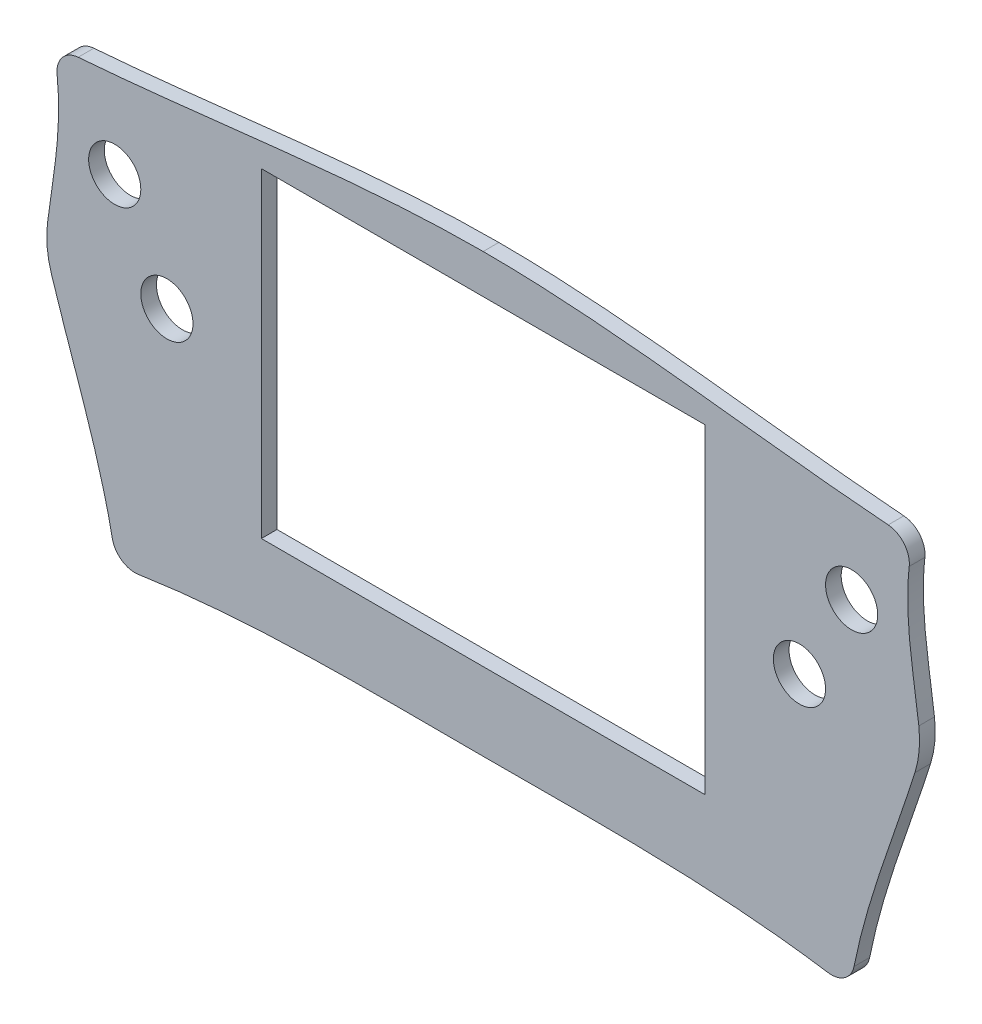
SolidWorks part; units mm, degrees
ref_plane "Front Plane" through (0, 0, 0) normal (0, 0, 1) x (1, 0, 0)
ref_plane "Top Plane" through (0, 0, 0) normal (0, 1, 0) x (1, 0, 0)
ref_plane "Right Plane" through (0, 0, 0) normal (1, 0, 0) x (0, 0, -1)
sketch "Sketch1" plane through (0, 0, 0) normal (0, 0, 1) x (1, 0, 0)
  line L0 (-89.6723, 78.6151) -> (-76.9723, 56.618) construction
  line L1 (-53.975, 97.6651) -> (53.975, 97.6651)
  line L2 (-53.975, 97.6651) -> (-53.975, 19.6871)
  line L3 (-53.975, 19.6871) -> (53.975, 19.6871)
  line L4 (53.975, 97.6651) -> (53.975, 19.6871)
  line L5 (77.0035, 56.618) -> (89.7035, 78.6151) construction
  line L6 (-1053.4632, 84.9651) -> (48946.5368, 84.9651) construction
  line L7 (-89.6723, 78.6151) -> (-98.1384, 93.2788) construction
  line L8 (89.7035, 78.6151) -> (98.1696, 93.2788) construction
  arc A0 (-90.9952, 1.4308) -> (-83.8129, -3.6021) centre (-84.7684, 2.6757) ccw construction
  arc A1 (91.0264, 1.4308) -> (83.8442, -3.6021) centre (84.7996, 2.6757) cw construction
  arc A2 (104.4808, 92.5779) -> (98.6567, 99.6101) centre (98.1696, 93.2788) ccw construction
  arc A3 (-104.4496, 92.5779) -> (-98.6254, 99.6101) centre (-98.1384, 93.2788) cw construction
  arc A4 (105.8354, 49.6367) -> (106.8178, 60.2997) centre (81.602, 57.2461) ccw construction
  arc A5 (-105.8042, 49.6367) -> (-106.7866, 60.2997) centre (-81.5708, 57.2461) cw construction
  arc A6 (-90.2479, 1.5802) -> (-83.9276, -2.8487) centre (-84.7684, 2.6757) ccw
  arc A7 (90.2792, 1.5802) -> (83.9588, -2.8487) centre (84.7996, 2.6757) cw
  arc A8 (105.1084, 49.865) -> (106.0613, 60.2081) centre (81.602, 57.2461) ccw
  arc A9 (103.7234, 92.662) -> (98.5982, 98.8503) centre (98.1696, 93.2788) ccw
  arc A10 (-103.6922, 92.662) -> (-98.567, 98.8503) centre (-98.1384, 93.2788) cw
  arc A11 (-105.0772, 49.865) -> (-106.0301, 60.2081) centre (-81.5708, 57.2461) cw
  circle A12 centre (-89.6723, 78.6151) radius 6.35
  circle A13 centre (89.7035, 78.6151) radius 6.35
  circle A14 centre (-76.9723, 56.618) radius 6.35
  circle A15 centre (77.0035, 56.618) radius 6.35
  spline S0 degree 3 poles (0, 0) (5.1735, 0.0127) (10.3471, 0.026) (15.5307, 0.04) (15.539, 0.04) (18.6201, 0.0483) (21.4623, 0.0491) (25.3867, 0.0393) (27.5771, 0.0304) (29.8788, 0.0136) (30.9717, 0.0034) (31.2425, 0.0008) (31.2454, 0.0007) (34.1264, -0.0278) (38.2682, -0.0931) (43.44, -0.2256) (45.9085, -0.3068) (47.1196, -0.3514) (47.1275, -0.3517) (49.962, -0.4562) (54.7735, -0.6793) (60.0041, -1.0158) (62.5414, -1.2072) (63.1737, -1.2567) (63.1822, -1.2573) (68.9953, -1.7129) (75.9402, -2.4511) (82.5675, -3.4078) (83.8442, -3.6021) knots 0 0 0 0 0.124756 0.124756 0.125 0.125 0.1875 0.1875 0.21875 0.242187 0.249878 0.249878 0.25 0.25 0.3125 0.34375 0.374756 0.374756 0.375 0.375 0.4375 0.484375 0.499756 0.499756 0.5 0.5 0.625 0.655173 0.655173 0.655173 0.655173 construction
  spline S1 degree 3 poles (-83.8129, -3.6021) (-82.5389, -3.4082) (-75.9152, -2.4519) (-68.9739, -1.7139) (-63.1502, -1.2573) (-63.132, -1.2559) (-60.6031, -1.0581) (-55.4198, -0.7108) (-49.9434, -0.4568) (-47.0982, -0.3518) (-47.0806, -0.3511) (-45.8695, -0.3066) (-43.4112, -0.2257) (-38.2513, -0.0934) (-34.1104, -0.028) (-31.2131, 0.0007) (-31.1984, 0.0009) (-30.1448, 0.0112) (-27.9298, 0.0283) (-25.463, 0.0383) (-21.5413, 0.0482) (-18.6702, 0.0477) (-15.5169, 0.04) (-15.4974, 0.0399) (-12.9014, 0.0336) (-10.3257, 0.0257) (-7.4256, 0.0151) (-7.1042, 0.014) (-4.5208, 0.0055) (-2.2604, 0.0012) (0, 0) knots 0.344884 0.344884 0.344884 0.344884 0.375 0.5 0.5 0.500488 0.500488 0.5625 0.625 0.625 0.625488 0.625488 0.65625 0.6875 0.75 0.75 0.750488 0.750488 0.78125 0.8125 0.8125 0.875 0.875 0.875488 0.875488 0.9375 0.9375 0.945312 0.945312 1 1 1 1 construction
  spline S2 degree 3 poles (91.0264, 1.4308) (93.358, 13.0932) (97.1393, 24.0412) (102.5678, 39.7371) (104.2841, 44.6964) (105.8354, 49.6367) knots -0.293558 -0.293558 -0.293558 -0.293558 0.5 0.5 0.87305 0.87305 0.87305 0.87305 construction
  spline S3 degree 3 poles (106.8178, 60.2997) (106.791, 60.5208) (106.7637, 60.7423) (106.4675, 63.1015) (105.8334, 67.4586) (105.1805, 71.989) (104.1938, 80.083) (103.7679, 86.159) (104.4808, 92.5779) knots 0.224038 0.224038 0.224038 0.224038 0.25 0.25 0.5 0.75 0.75 1.37521 1.37521 1.37521 1.37521 construction
  spline S4 degree 3 poles (98.6567, 99.6101) (97.303, 99.7142) (95.9504, 99.8237) (83.9121, 100.8408) (62.6582, 103.2369) (41.6376, 105.6033) (20.7362, 107.3693) (10.3458, 107.9521) (0.0156, 107.9521) knots 0.218379 0.218379 0.218379 0.218379 0.25 0.25 0.5 0.75 0.75 1 1 1 1 construction
  spline S5 degree 3 poles (0.0156, 107.9521) (-10.3146, 107.9521) (-20.705, 107.3693) (-41.6063, 105.6033) (-62.627, 103.2369) (-83.8808, 100.8408) (-95.9191, 99.8237) (-97.2718, 99.7142) (-98.6254, 99.6101) knots 0 0 0 0 0.25 0.25 0.5 0.75 0.75 0.781621 0.781621 0.781621 0.781621 construction
  spline S6 degree 3 poles (-105.8042, 49.6367) (-104.2529, 44.6964) (-102.5366, 39.7371) (-97.108, 24.0412) (-93.3267, 13.0932) (-90.9952, 1.4308) knots 0.12695 0.12695 0.12695 0.12695 0.5 0.5 1.293558 1.293558 1.293558 1.293558 construction
  spline S7 degree 3 poles (-104.4496, 92.5779) (-103.7367, 86.159) (-104.1626, 80.083) (-105.1492, 71.989) (-105.8022, 67.4586) (-106.4363, 63.1015) (-106.7325, 60.7423) (-106.7598, 60.5208) (-106.7866, 60.2997) knots -0.37521 -0.37521 -0.37521 -0.37521 0.25 0.25 0.5 0.75 0.75 0.775962 0.775962 0.775962 0.775962 construction
  spline S8 degree 1 poles (-83.9276, -2.8487) (-0.0007, 0.762) knots 0 0 1 1 construction
  spline S9 degree 1 poles (-0.0007, 0.762) (83.9588, -2.8487) knots 0 0 1 1 construction
  spline S10 degree 1 poles (90.2792, 1.5802) (105.1084, 49.865) knots 0 0 1 1 construction
  spline S11 degree 1 poles (106.0613, 60.2081) (103.7234, 92.662) knots 0 0 1 1 construction
  spline S12 degree 1 poles (98.5982, 98.8503) (0.0156, 107.1901) knots 0 0 1 1 construction
  spline S13 degree 1 poles (0.0156, 107.1901) (-98.567, 98.8503) knots 0 0 1 1 construction
  spline S14 degree 1 poles (-103.6922, 92.662) (-106.0301, 60.2081) knots 0 0 1 1 construction
  spline S15 degree 1 poles (-105.0772, 49.865) (-90.2479, 1.5802) knots 0 0 1 1 construction
  spline S16 degree 3 poles (-83.9276, -2.8487) (-83.0541, -2.7158) (-81.3127, -2.4601) (-78.6543, -2.0975) (-75.9665, -1.7582) (-72.337, -1.3362) (-68.6439, -0.9599) (-65.584, -0.6905) (-64.1668, -0.5737) (-63.5661, -0.5256) (-63.1042, -0.4893) (-62.6999, -0.458) (-61.9625, -0.4018) (-60.9159, -0.3251) (-59.2176, -0.2068) (-57.0682, -0.0687) (-54.4397, 0.082) (-51.767, 0.2174) (-49.4909, 0.318) (-48.009, 0.3766) (-47.3036, 0.4032) (-46.8762, 0.4189) (-46.1962, 0.4433) (-45.1759, 0.478) (-43.5402, 0.5294) (-41.4429, 0.5878) (-38.8565, 0.648) (-36.1958, 0.6983) (-33.9194, 0.7322) (-32.4068, 0.7502) (-31.7062, 0.7578) (-31.4084, 0.7608) (-31.1812, 0.7631) (-31.0214, 0.7646) (-30.7077, 0.7676) (-30.2699, 0.7715) (-29.5464, 0.7775) (-28.6196, 0.7841) (-27.465, 0.791) (-25.8712, 0.7987) (-23.7764, 0.8053) (-21.0954, 0.8088) (-18.7302, 0.8079) (-16.9889, 0.8052) (-16.1182, 0.8034) (-15.5864, 0.8022) (-15.1606, 0.8011) (-14.6294, 0.7998) (-13.7789, 0.7975) (-12.2906, 0.7934) (-10.1656, 0.787) (-7.6097, 0.7776) (-4.2329, 0.7667) (-1.6926, 0.7629) (-0.0007, 0.762) knots 0.344884 0.344884 0.344884 0.344884 0.365356 0.385828 0.4063 0.426772 0.467716 0.488188 0.493306 0.498424 0.500984 0.503543 0.508661 0.518897 0.529133 0.549605 0.570077 0.590549 0.611021 0.621257 0.623816 0.626375 0.631493 0.641729 0.651965 0.672437 0.692909 0.713381 0.733854 0.74409 0.746649 0.749208 0.750487 0.751767 0.754326 0.759444 0.764562 0.774798 0.785034 0.79527 0.815742 0.836214 0.856686 0.866922 0.87204 0.874599 0.877158 0.882276 0.887394 0.89763 0.918102 0.938575 0.959047 0.999991 0.999991 0.999991 0.999991
  spline S17 degree 3 poles (-0.0007, 0.762) (1.6973, 0.7662) (4.2444, 0.7725) (7.6405, 0.7812) (10.1877, 0.7878) (12.3099, 0.7934) (13.7963, 0.7973) (14.6443, 0.7996) (15.1776, 0.801) (15.5967, 0.8022) (16.1183, 0.8035) (16.974, 0.8055) (18.6883, 0.8084) (21.028, 0.8096) (23.6979, 0.8063) (25.7999, 0.7996) (27.4093, 0.7918) (28.5803, 0.7848) (29.5252, 0.778) (30.265, 0.7719) (30.7153, 0.7679) (31.0358, 0.7648) (31.2033, 0.7632) (31.4247, 0.761) (31.7255, 0.7579) (32.4247, 0.7504) (33.9391, 0.7323) (36.2152, 0.6986) (38.8771, 0.6482) (41.4644, 0.5881) (43.5624, 0.5297) (45.1991, 0.4783) (46.219, 0.4436) (46.9009, 0.4192) (47.3259, 0.4035) (48.0323, 0.377) (49.5136, 0.3184) (51.7907, 0.2178) (54.4639, 0.0824) (57.0932, -0.0683) (59.2433, -0.2064) (60.9421, -0.3247) (61.9892, -0.4015) (62.7268, -0.4576) (63.1316, -0.489) (63.5924, -0.5252) (64.1937, -0.5734) (65.6109, -0.6901) (68.6718, -0.9595) (72.3655, -1.3358) (75.9958, -1.758) (78.6842, -2.0973) (81.3433, -2.46) (83.0851, -2.7158) (83.9588, -2.8487) knots 0.000009 0.000009 0.000009 0.000009 0.040957 0.061431 0.081905 0.102378 0.112615 0.117734 0.122852 0.125412 0.127971 0.133089 0.143326 0.1638 0.184274 0.204748 0.214985 0.225222 0.235459 0.240577 0.245696 0.248255 0.249534 0.250814 0.253373 0.255932 0.266169 0.286643 0.307117 0.327591 0.348065 0.358302 0.368539 0.373657 0.376216 0.378776 0.389013 0.409486 0.42996 0.450434 0.470908 0.481145 0.491382 0.4965 0.49906 0.501619 0.506737 0.511856 0.53233 0.573277 0.593751 0.614225 0.634699 0.655173 0.655173 0.655173 0.655173
  spline S18 degree 3 poles (90.2792, 1.5802) (90.7073, 3.7213) (91.6711, 8.0016) (93.9035, 16.3317) (97.1434, 26.4672) (100.5871, 36.3067) (103.2449, 44.085) (104.5003, 47.9284) (105.1084, 49.865) knots -0.293558 -0.293558 -0.293558 -0.293558 -0.147732 -0.001906 0.289746 0.581398 0.727224 0.87305 0.87305 0.87305 0.87305
  spline S19 degree 3 poles (106.0613, 60.2081) (105.9117, 61.4441) (105.584, 63.8876) (104.8451, 68.9626) (103.9069, 75.5268) (103.3306, 82.4483) (103.3452, 87.4908) (103.5043, 90.4232) (103.641, 91.9197) (103.7234, 92.662) knots 0.224038 0.224038 0.224038 0.224038 0.367934 0.511831 0.799624 1.087417 1.231313 1.303262 1.37521 1.37521 1.37521 1.37521
  spline S20 degree 3 poles (98.5982, 98.8503) (94.4161, 99.172) (86.05, 99.9192) (69.4226, 101.6741) (48.7792, 104.0869) (28.3446, 106.0814) (12.109, 107.0125) (4.0527, 107.1901) (0.0156, 107.1901) knots 0.218379 0.218379 0.218379 0.218379 0.316081 0.413784 0.609189 0.804595 0.902297 1 1 1 1
  spline S21 degree 3 poles (0.0156, 107.1901) (-4.0215, 107.1901) (-12.0778, 107.0125) (-28.3134, 106.0814) (-48.7479, 104.0869) (-69.3913, 101.6741) (-86.0187, 99.9192) (-94.3849, 99.172) (-98.567, 98.8503) knots 0 0 0 0 0.097703 0.195405 0.390811 0.586216 0.683919 0.781621 0.781621 0.781621 0.781621
  spline S22 degree 3 poles (-103.6922, 92.662) (-103.6098, 91.9197) (-103.4731, 90.4232) (-103.314, 87.4908) (-103.2994, 82.4483) (-103.8757, 75.5268) (-104.8139, 68.9626) (-105.5527, 63.8876) (-105.8804, 61.4441) (-106.0301, 60.2081) knots -0.37521 -0.37521 -0.37521 -0.37521 -0.303262 -0.231313 -0.087417 0.200376 0.488169 0.632066 0.775962 0.775962 0.775962 0.775962
  spline S23 degree 3 poles (-105.0772, 49.865) (-104.4691, 47.9284) (-103.2137, 44.085) (-100.5558, 36.3067) (-97.1121, 26.4672) (-93.8723, 16.3317) (-91.6399, 8.0016) (-90.676, 3.7213) (-90.2479, 1.5802) knots 0.12695 0.12695 0.12695 0.12695 0.272776 0.418602 0.710254 1.001906 1.147732 1.293558 1.293558 1.293558 1.293558
  point P53 (-93.3384, 84.9651)
  dimension "D1" = 6.35
  dimension "D2" = 25.4
  dimension "D9" = 12.7
  dimension "D10" = 12.7
  dimension "D11" = 12.7
  dimension "D12" = 12.7
  dimension "D4" = 107.95
  dimension "D5" = 77.978
  dimension "D6" = 53.975
  dimension "D7" = 9.525
  dimension "D8" = 30
  dimension "D13" = 30
  dimension "D14" = 12.7
  dimension "D15" = 25.4
  dimension "D16" = 25.4
  dimension "D3" = 0.762
extrude "Boss-Extrude1" add sketch "Sketch1" along normal blind 3.81
